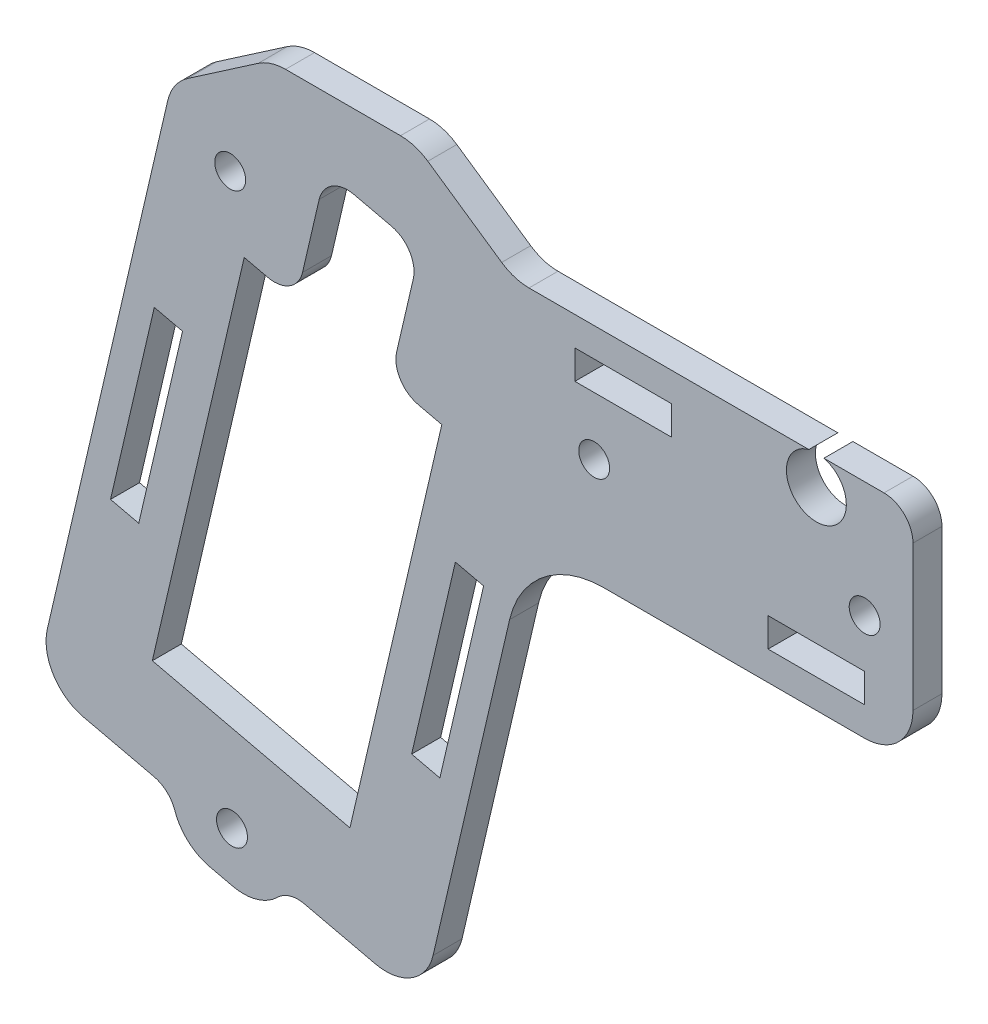
SolidWorks part; units mm, degrees
material "MDF"
ref_plane "Plano frontal" through (0, 0, 0) normal (0, 0, 1) x (1, 0, 0)
ref_plane "Plano superior" through (0, 0, 0) normal (0, 1, 0) x (1, 0, 0)
ref_plane "Plano direito" through (0, 0, 0) normal (1, 0, 0) x (0, 0, -1)
sketch "Esboço1" plane through (0, 0, 0) normal (0, 0, 1) x (1, 0, 0)
  line L0 (0, 20) -> (0, 0) construction
  line L5 (10, 16) -> (13, 16) construction
  line L6 (13, 6) -> (13, 16) construction
  line L15 (5, 11) -> (-10, 11) construction
  line L16 (10, 6) -> (13, 6) construction
  line L21 (-10, 6) -> (-13, 6) construction
  line L22 (-10, 6) -> (-10, 16) construction
  line L27 (-10, 16) -> (-13, 16) construction
  line L28 (-13, 6) -> (-13, 16) construction
  line L29 (-10, 6) -> (-13, 16) construction
  line L30 (-10, 16) -> (-13, 6) construction
  line L35 (10, 6) -> (10, 16) construction
  line L36 (18, 0) -> (18, 23)
  line L37 (18, 23) -> (-66.701, 23)
  line L43 (-29.9553, 0) -> (18, 0)
  line L61 (-68.7379, -29.9136) -> (-59.2257, 10.995)
  line L66 (-59.2257, 10.995) -> (-38.7714, 6.2389)
  line L67 (-38.7714, 6.2389) -> (-48.2836, -34.6697)
  line L68 (-48.2836, -34.6697) -> (-68.7379, -29.9136)
  line L69 (-63.9818, -9.4593) -> (-43.5275, -14.2154) construction
  line L74 (-48.9985, 8.617) -> (-58.5107, -32.2917) construction
  line L75 (-61.7051, 0.3321) -> (-41.2508, -4.424) construction
  line L80 (-38.7714, 6.2389) -> (-38.7714, -27.2218) construction
  line L85 (0, 20) -> (-15.8727, -48.263) construction
  line L86 (5, 3) -> (-5, 3)
  line L87 (-66.701, 23) -> (-80.7429, -37.389)
  line L88 (-80.7429, -37.389) -> (-40.8082, -46.6747)
  line L89 (-40.8082, -46.6747) -> (-29.9553, 0)
  line L93 (-65.6456, -40.8994) -> (-66.4949, -44.552)
  line L94 (-66.4949, -44.552) -> (-56.7548, -46.8168)
  line L95 (-55.9055, -43.1642) -> (-56.7548, -46.8168)
  line L96 (-47.0168, 17.1396) -> (-48.1492, 12.2695) construction
  line L97 (-48.1492, 12.2695) -> (-53.0193, 13.4019) construction
  line L98 (5, 3) -> (5, 6)
  line L99 (5, 6) -> (-5, 6)
  line L100 (-5, 3) -> (-5, 6)
  line L101 (0, 6) -> (0, 0) construction
  line L102 (5, 4.5) -> (-5, 4.5) construction
  line L103 (10, 0) -> (10, 23)
  line L104 (-73.0647, -17.6141) -> (-70.1427, -18.2935)
  line L105 (-70.1427, -18.2935) -> (-65.6131, 1.1868)
  line L106 (-65.6131, 1.1868) -> (-68.5351, 1.8662)
  line L107 (-38.9742, -25.5409) -> (-41.8962, -24.8615)
  line L108 (-37.3666, -5.3812) -> (-34.4446, -6.0606)
  line L109 (-41.8962, -24.8615) -> (-37.3666, -5.3812)
  line L115 (-53.8686, 9.7494) -> (-50.7875, 23)
  line L116 (-50.7875, 23) -> (-41.0474, 20.7352)
  line L117 (-25, 17) -> (-15, 17)
  line L118 (-25, 17) -> (-25, 20)
  line L119 (-25, 20) -> (-15, 20)
  line L120 (-15, 17) -> (-15, 20)
  line L121 (-20, 20) -> (-20, 17) construction
  line L122 (-25, 18.5) -> (-15, 18.5) construction
  line L123 (-68.5351, 1.8662) -> (-73.0647, -17.6141)
  line L124 (-38.9742, -25.5409) -> (-34.4446, -6.0606)
  line L125 (-41.0474, 20.7352) -> (-44.1285, 7.4846)
  line L126 (-66.701, 23) -> (-56.4985, 30)
  line L127 (-56.4985, 30) -> (-41.4985, 30)
  line L128 (-41.4985, 30) -> (-31.296, 23)
  circle A0 centre (0, 20) radius 7.5 construction
  circle A1 centre (5, 11) radius 1.6
  circle A2 centre (-10, 11) radius 1.6 construction
  circle A8 centre (-64.2301, -34.8118) radius 1.6 construction
  circle A9 centre (-54.49, -37.0766) radius 1.6 construction
  circle A10 centre (-43.2792, 11.1371) radius 1.6 construction
  circle A11 centre (-53.0193, 13.4019) radius 1.6 construction
  circle A12 centre (-47.0168, 17.1396) radius 1.6 construction
  circle A15 centre (-60.4925, -40.8143) radius 1.6
  circle A16 centre (-23, 11) radius 1.6
  circle A17 centre (-60.6769, 18) radius 1.6
  circle A18 centre (0, 20) radius 3.1
  point P0 (0, 20)
  point P13 (-11.5, 11)
  point P39 (-51.4779, -2.046)
  point P49 (0, 4.5)
  point P56 (-67.8779, -8.5534)
  point P61 (0, 11)
  point P72 (-20, 18.5)
  point P82 (-45.9175, 21.8676)
  point P85 (-48.9985, 30)
  point P90 (0, 23.1)
  point P91 (0, 26.1)
  dimension "D1" = 15
  dimension "D3" = 3.2
  dimension "D11" = 14.6974
  dimension "D12" = 56
  dimension "D9" = 49.5
  dimension "D30" = 5
  dimension "D31" = 5
  dimension "D28" = 10
  dimension "D35" = 7
  dimension "D36" = 5
  dimension "D25" = 6.2
  dimension "D2" = 15
  dimension "D4" = 5
  dimension "D5" = 21
  dimension "D6" = 10
  dimension "D7" = 3
  dimension "D8" = 42
  dimension "D10" = 10
  dimension "D13" = 20
  dimension "D14" = 5
  dimension "D15" = 10
  dimension "D16" = 10
  dimension "D17" = 6
  dimension "D18" = 5
  dimension "D19" = 7
  dimension "D20" = 5
  dimension "D21" = 13.09
  dimension "D22" = 10
  dimension "D23" = 10
  dimension "D24" = 10
  dimension "D26" = 3
  dimension "D27" = 20
  dimension "D29" = 10
  dimension "D32" = 7
  dimension "D33" = 5
  dimension "D34" = 4
  dimension "D37" = 15
  dimension "D38" = 3
  dimension "D39" = 3
  dimension "D40" = 3
extrude "Ressalto-extrusão1" add sketch "Esboço1" along normal blind 3
fillet "Filete1" radius 5 3 edges at (-40.8082, -46.6747, 1.5) (-80.7429, -37.389, 1.5) (10, 0, 1.5)
fillet "Filete3" radius 3 7 edges at (-65.6456, -40.8994, 1.5) (-55.9055, -43.1642, 1.5) (10, 23, 1.5) (-50.7875, 23, 1.5) (-41.0474, 20.7352, 1.5) (-44.1285, 7.4846, 1.5) (-53.8686, 9.7494, 1.5)
fillet "Filete4" radius 10 1 edges at (-29.9553, 0, 1.5)
fillet "Filete2" radius 5 6 edges at (-56.7548, -46.8168, 1.5) (-66.4949, -44.552, 1.5) (-31.296, 23, 1.5) (-41.4985, 30, 1.5) (-56.4985, 30, 1.5) (-66.701, 23, 1.5)
